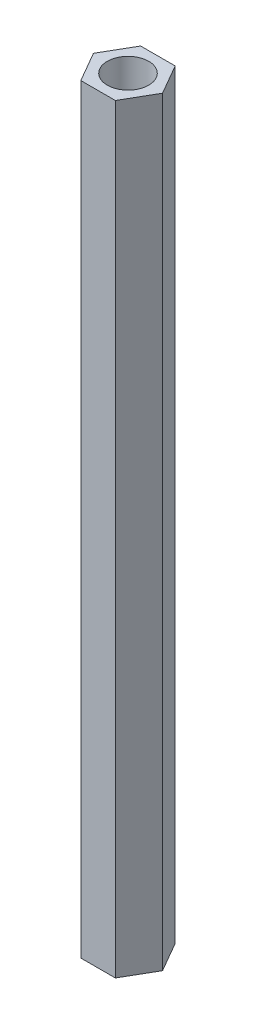
SolidWorks part; units mm, degrees
material "黄铜"
ref_plane "前视基准面" through (0, 0, 0) normal (0, 0, 1) x (1, 0, 0)
ref_plane "上视基准面" through (0, 0, 0) normal (0, 1, 0) x (1, 0, 0)
ref_plane "右视基准面" through (0, 0, 0) normal (1, 0, 0) x (0, 0, -1)
sketch "草图1" plane through (0, 0, 0) normal (0, 1, 0) x (1, 0, 0)
  line L1 (-2.5, 0) -> (-1.25, -2.1651)
  line L2 (-1.25, -2.1651) -> (1.25, -2.1651)
  line L3 (1.25, -2.1651) -> (2.5, 0)
  line L4 (2.5, 0) -> (1.25, 2.1651)
  line L5 (1.25, 2.1651) -> (-1.25, 2.1651)
  line L6 (-1.25, 2.1651) -> (-2.5, 0)
  circle A0 centre (0, 0) radius 2.1651 construction
  circle A1 centre (0, 0) radius 1.5
  dimension "D2" = 3
  dimension "D1" = 2.5
extrude "凸台-拉伸1" add sketch "草图1" along normal blind 55
